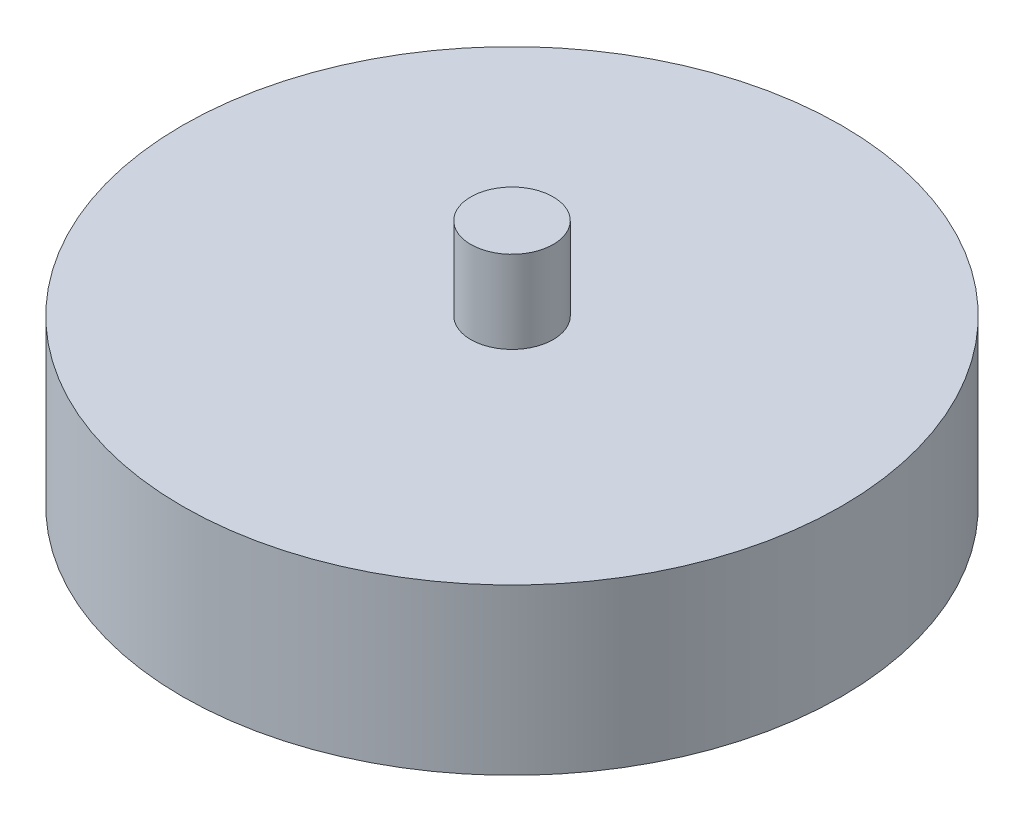
SolidWorks part; units mm, degrees
material "Acrylic (Medium-high impact)"
ref_plane "Front Plane" through (0, 0, 0) normal (0, 0, 1) x (1, 0, 0)
ref_plane "Top Plane" through (0, 0, 0) normal (0, 1, 0) x (1, 0, 0)
ref_plane "Right Plane" through (0, 0, 0) normal (1, 0, 0) x (0, 0, -1)
sketch "Sketch1" plane through (0, 0, 0) normal (0, 1, 0) x (1, 0, 0)
  circle A0 centre (0, 0) radius 101.6
  dimension "D1" = 203.2
extrude "Boss-Extrude1" add sketch "Sketch1" along normal blind 50.8
sketch "Sketch2" plane through (0, 50.8, 0) normal (0, 1, 0) x (1, 0, 0)
  circle A0 centre (0, 0) radius 12.7
  dimension "D1" = 25.4
extrude "Boss-Extrude2" add sketch "Sketch2" along normal blind 25.4 contours A0
